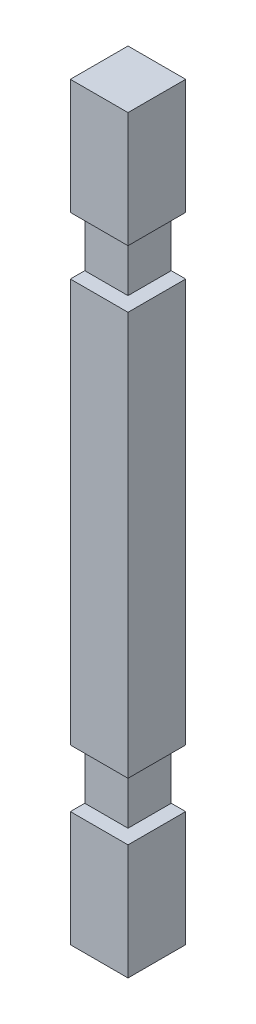
SolidWorks part; units mm, degrees
material "Balsa"
ref_plane "Front Plane" through (0, 0, 0) normal (0, 0, 1) x (1, 0, 0)
ref_plane "Top Plane" through (0, 0, 0) normal (0, 1, 0) x (1, 0, 0)
ref_plane "Right Plane" through (0, 0, 0) normal (1, 0, 0) x (0, 0, -1)
sketch "Sketch2" plane through (0, 0, 0) normal (0, 0, 1) x (1, 0, 0)
  line L0 (0, 330.2) -> (0, -330.2) construction
  line L1 (-25.4, 330.2) -> (25.4, 330.2)
  line L2 (-25.4, 330.2) -> (-25.4, -330.2)
  line L3 (-25.4, -330.2) -> (25.4, -330.2)
  line L4 (25.4, 330.2) -> (25.4, -330.2)
  line L5 (-25.4, 0) -> (25.4, 0) construction
  dimension "D1" = 50.8
  dimension "D2" = 660.4
extrude "Boss-Extrude1" add sketch "Sketch2" along normal blind 50.8
sketch "Sketch5" plane through (0, 0, 50.8) normal (0, 0, 1) x (1, 0, 0)
  line L0 (-25.4, 330.2) -> (-25.4, -330.2) construction
  line L1 (-25.4, 228.6) -> (25.4, 228.6)
  line L2 (-25.4, 228.6) -> (-25.4, 177.8)
  line L3 (-25.4, 177.8) -> (25.4, 177.8)
  line L4 (25.4, 228.6) -> (25.4, 177.8)
  line L5 (25.4, -330.2) -> (25.4, 330.2) construction
  line L6 (25.4, 330.2) -> (-25.4, 330.2) construction
  dimension "D1" = 50.8
  dimension "D2" = 101.6
extrude "Cut-Extrude1" cut sketch "Sketch5" against normal blind 12.7
sketch "Sketch6" plane through (25.4, 0, 0) normal (1, 0, 0) x (0, 0, -1)
  line L0 (0, -330.2) -> (0, 330.2) construction
  line L1 (-50.8, 228.6) -> (0, 228.6)
  line L2 (-50.8, 228.6) -> (-50.8, 177.8)
  line L3 (-50.8, 177.8) -> (0, 177.8)
  line L4 (0, 228.6) -> (0, 177.8)
  dimension "D1" = 50.8
extrude "Cut-Extrude2" cut sketch "Sketch6" against normal blind 12.7
sketch "Sketch10" plane through (0, 0, 50.8) normal (0, 0, 1) x (1, 0, 0)
  line L0 (25.4, -330.2) -> (25.4, 177.8) construction
  line L1 (25.4, -177.8) -> (-25.4, -177.8)
  line L2 (25.4, -177.8) -> (25.4, -228.6)
  line L3 (25.4, -228.6) -> (-25.4, -228.6)
  line L4 (-25.4, -177.8) -> (-25.4, -228.6)
  line L5 (-25.4, 177.8) -> (-25.4, -330.2) construction
  line L6 (-25.4, -330.2) -> (25.4, -330.2) construction
  dimension "D1" = 50.8
  dimension "D2" = 101.6
extrude "Cut-Extrude3" cut sketch "Sketch10" against normal blind 12.7
sketch "Sketch11" plane through (25.4, 0, 0) normal (1, 0, 0) x (0, 0, -1)
  line L0 (0, -330.2) -> (0, 177.8) construction
  line L1 (-50.8, -177.8) -> (0, -177.8)
  line L2 (-50.8, -177.8) -> (-50.8, -228.6)
  line L3 (-50.8, -228.6) -> (0, -228.6)
  line L4 (0, -177.8) -> (0, -228.6)
  dimension "D1" = 50.8
extrude "Cut-Extrude4" cut sketch "Sketch11" against normal blind 12.7
sketch "Sketch12" plane through (0, 0, 0) normal (0, 0, -1) x (-1, 0, 0)
  line L0 (-25.4, 330.2) -> (25.4, 330.2) construction
  line L1 (-25.4, 228.6) -> (-25.4, 330.2) construction
  circle A0 centre (0, 304.8) radius 8
  point P4 (0, 330.2)
  dimension "D1" = 25.4
  dimension "D3" = 16
  dimension "D2" = 25.4
extrude "Cut-Extrude5" cut sketch "Sketch12" against normal blind 16
sketch "Sketch13" plane through (-25.4, 0, 0) normal (-1, 0, 0) x (0, 0, 1)
  line L0 (50.8, 330.2) -> (0, 330.2) construction
  line L1 (50.8, 330.2) -> (50.8, 228.6) construction
  circle A0 centre (25.4, 304.8) radius 8
  dimension "D1" = 16
  dimension "D2" = 25.4
  dimension "D3" = 25.4
extrude "Cut-Extrude6" cut sketch "Sketch13" against normal blind 16
sketch "Sketch14" plane through (0, 0, 0) normal (0, 0, -1) x (-1, 0, 0)
  line L0 (25.4, -330.2) -> (-25.4, -330.2) construction
  line L1 (-25.4, -330.2) -> (-25.4, -228.6) construction
  circle A0 centre (0, -304.8) radius 8
  dimension "D1" = 16
  dimension "D2" = 25.4
  dimension "D3" = 25.4
extrude "Cut-Extrude7" cut sketch "Sketch14" against normal blind 16
sketch "Sketch15" plane through (-25.4, 0, 0) normal (-1, 0, 0) x (0, 0, 1)
  line L0 (50.8, -330.2) -> (0, -330.2) construction
  line L1 (50.8, -228.6) -> (50.8, -330.2) construction
  circle A0 centre (25.4, -304.8) radius 8
  dimension "D1" = 16
  dimension "D2" = 25.4
  dimension "D3" = 25.4
extrude "Cut-Extrude8" cut sketch "Sketch15" against normal blind 16
